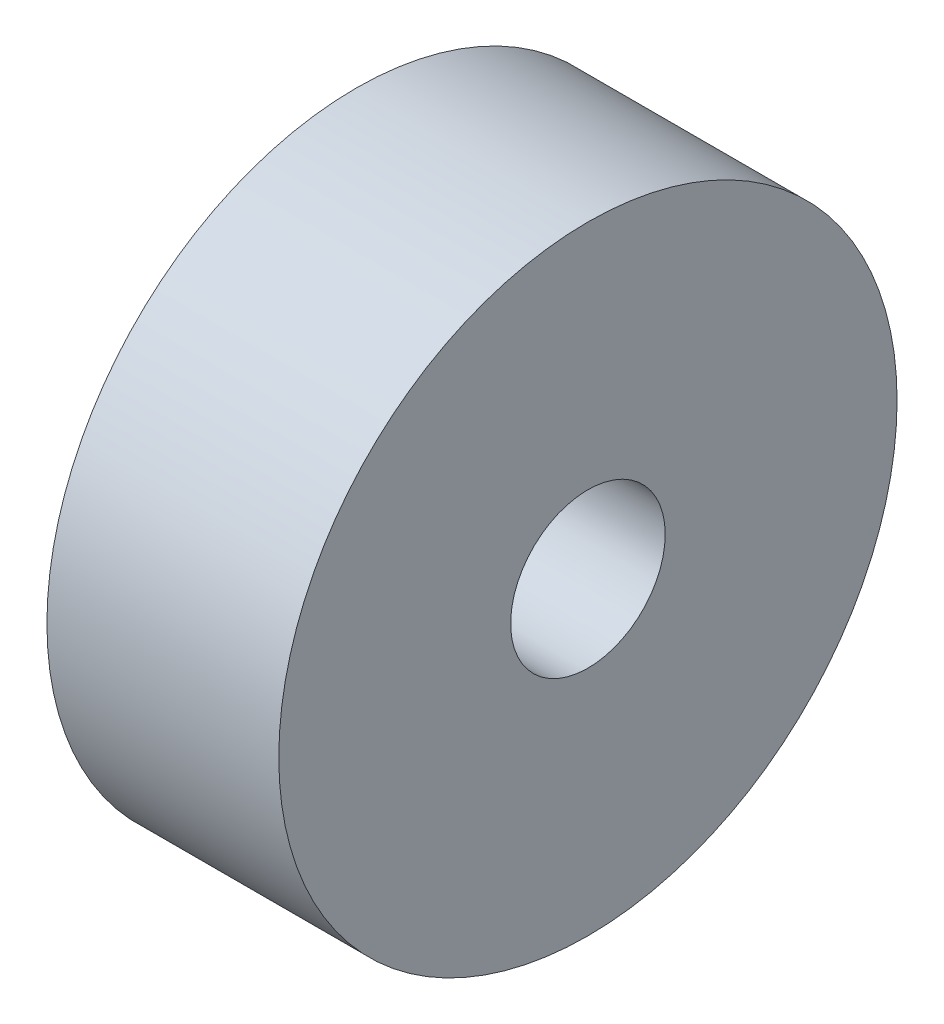
SolidWorks part; units mm, degrees
material "POLYURETHANE (11671)"
ref_plane "Front" through (0, 0, 0) normal (0, 0, 1) x (1, 0, 0)
ref_plane "Top" through (0, 0, 0) normal (0, 1, 0) x (1, 0, 0)
ref_plane "Right" through (0, 0, 0) normal (1, 0, 0) x (0, 0, -1)
sketch "Sketch1" plane through (0, 0, 0) normal (1, 0, 0) x (0, 0, -1)
  circle A0 centre (0, 0) radius 101.6
  circle A1 centre (0, 0) radius 25.4
  dimension "D1" = 50.8
  dimension "D2" = 203.2
extrude "Boss-Extrude1" add sketch "Sketch1" along normal blind 76.2
